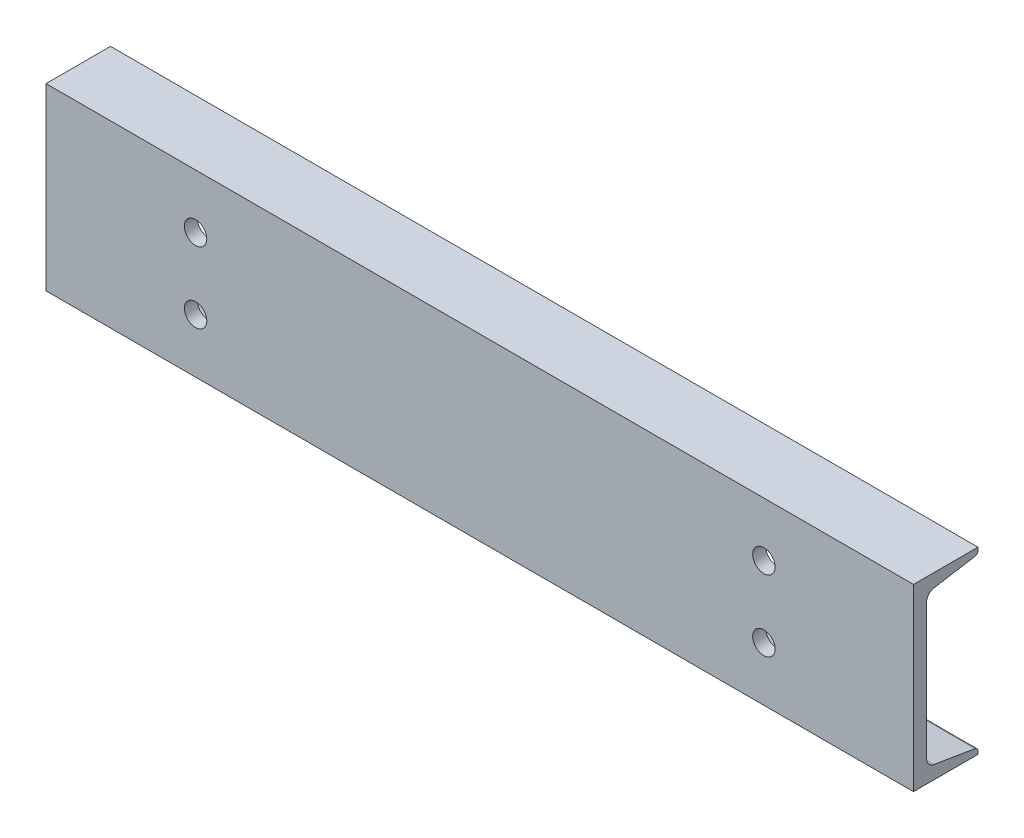
SolidWorks part; units mm, degrees
ref_plane "Front Plane" through (0, 0, 0) normal (0, 0, 1) x (1, 0, 0)
ref_plane "Top Plane" through (0, 0, 0) normal (0, 1, 0) x (1, 0, 0)
ref_plane "Right Plane" through (0, 0, 0) normal (1, 0, 0) x (0, 0, -1)
sketch "Sketch1" plane through (0, 0, 0) normal (1, 0, 0) x (0, 0, -1)
  line L0 (-27.3939, -76.2) -> (-27.3939, 76.2)
  line L1 (-27.3939, 76.2) -> (27.3939, 76.2)
  line L2 (-27.3939, -76.2) -> (27.3939, -76.2)
  line L3 (4.3561, -67.4878) -> (-21.0439, -67.4878) construction
  line L4 (-16.2941, 57.3918) -> (-16.2941, -57.3918)
  line L5 (27.3939, 76.2) -> (27.3939, 73.7107)
  line L6 (27.3939, -76.2) -> (27.3939, -73.7107)
  line L7 (-9.9269, 64.9081) -> (24.847, 70.7042)
  line L8 (-9.9269, -64.9081) -> (24.847, -70.7042)
  arc A0 (-16.2941, -57.3918) -> (-9.9269, -64.9081) centre (-8.6741, -57.3918) ccw
  arc A1 (-16.2941, 57.3918) -> (-9.9269, 64.9081) centre (-8.6741, 57.3918) cw
  arc A2 (27.3939, 73.7107) -> (24.847, 70.7042) centre (24.3459, 73.7107) cw
  arc A3 (27.3939, -73.7107) -> (24.847, -70.7042) centre (24.3459, -73.7107) ccw
extrude "Boss-Extrude1" add sketch "Sketch1" along normal mid plane 736.6
sketch "Sketch2" plane through (0, -76.2, 0) normal (0, -1, 0) x (1, 0, 0)
  line L0 (0, -27.3939) -> (0, 27.3939) construction
  line L1 (368.3, -27.3939) -> (-368.3, -27.3939) construction
  line L2 (368.3, 27.3939) -> (-368.3, 27.3939) construction
  line L3 (-7.7616, -7.5311) -> (387.7777, -7.5311) construction
  line L4 (368.3, 27.3939) -> (368.3, -27.3939) construction
  circle A0 centre (190.5, -7.5311) radius 9.525
  circle A1 centre (-190.5, -7.5311) radius 9.525
  circle A2 centre (330.2, -7.5311) radius 9.525
  circle A3 centre (-330.2, -7.5311) radius 9.525
  dimension "D2" = 19.05
  dimension "D4" = 38.1
  dimension "D1" = 34.925
  dimension "D3" = 177.8
extrude "Cut-Extrude1" cut sketch "Sketch2" against normal up to next
sketch "Sketch3" plane through (0, 0, 27.3939) normal (0, 0, 1) x (1, 0, 0)
  line L0 (368.3, 76.2) -> (368.3, -76.2) construction
  line L1 (368.3, -76.2) -> (-368.3, -76.2) construction
  line L2 (368.3, 0) -> (-368.3, 0) construction
  line L3 (-368.3, 76.2) -> (-368.3, -76.2) construction
  line L4 (0, -76.2) -> (0, 76.2) construction
  line L5 (368.3, 76.2) -> (-368.3, 76.2) construction
  circle A0 centre (241.3, -30.1625) radius 9.525
  circle A1 centre (-241.3, -30.1625) radius 9.525
  circle A2 centre (-241.3, 30.1625) radius 9.525
  circle A3 centre (241.3, 30.1625) radius 9.525
  dimension "D3" = 19.05
  dimension "D1" = 127
  dimension "D2" = 46.0375
extrude "Cut-Extrude2" cut sketch "Sketch3" against normal up to next
